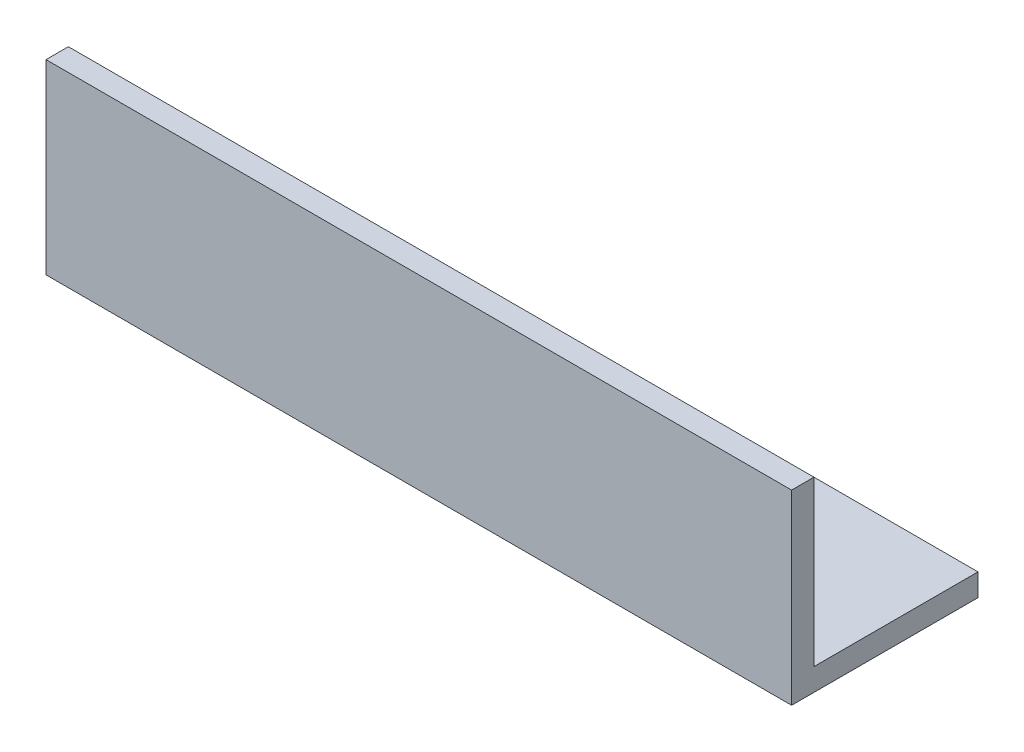
SolidWorks part; units mm, degrees
ref_plane "Спереди" through (0, 0, 0) normal (0, 0, 1) x (1, 0, 0)
ref_plane "Сверху" through (0, 0, 0) normal (0, 1, 0) x (1, 0, 0)
ref_plane "Справа" through (0, 0, 0) normal (1, 0, 0) x (0, 0, -1)
sketch "Эскиз1" plane through (0, 0, 0) normal (1, 0, 0) x (0, 0, -1)
  line L0 (0, 25) -> (0, 0)
  line L1 (0, 0) -> (25, 0)
extrude "Вытянуть-Тонкостенный1" add sketch "Эскиз1" along normal blind 100 thin thin type one direction reverse wall 3
